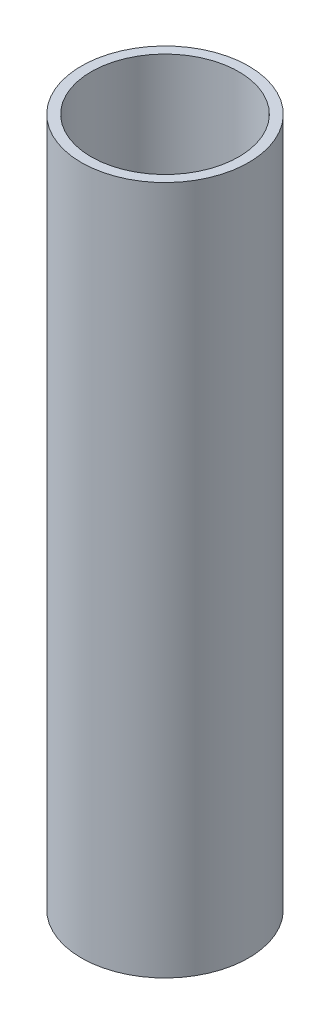
SolidWorks part; units mm, degrees
ref_plane "Front Plane" through (0, 0, 0) normal (0, 0, 1) x (1, 0, 0)
ref_plane "Top Plane" through (0, 0, 0) normal (0, 1, 0) x (1, 0, 0)
ref_plane "Right Plane" through (0, 0, 0) normal (1, 0, 0) x (0, 0, -1)
sketch "Sketch1" plane through (0, 0, 0) normal (0, 1, 0) x (1, 0, 0)
  circle A0 centre (0, 0) radius 15
  circle A1 centre (0, 0) radius 17
  dimension "D1" = 30
  dimension "D2" = 2
extrude "Boss-Extrude1" add sketch "Sketch1" along normal blind 140
